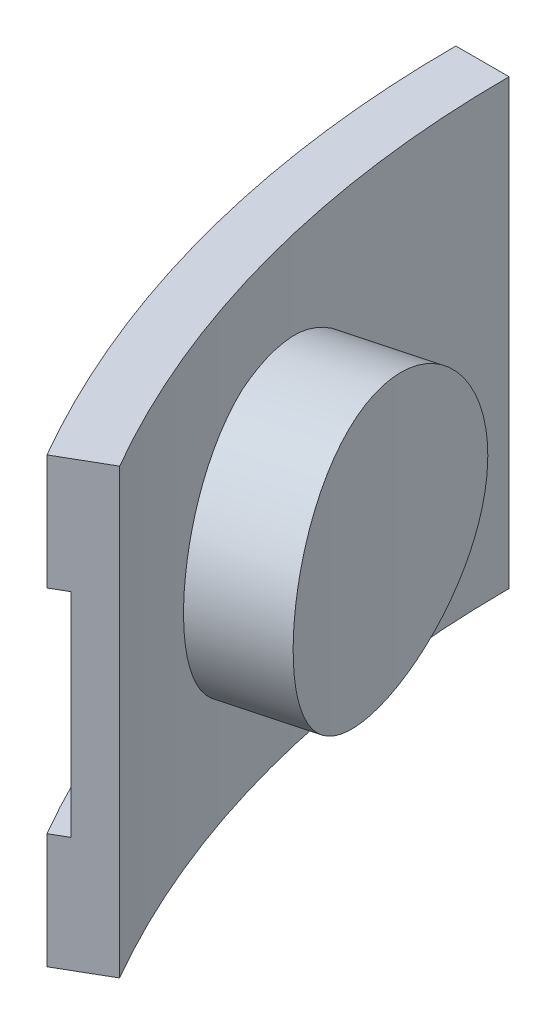
SolidWorks part; units mm, degrees
ref_plane "Front Plane" through (0, 0, 0) normal (0, 0, 1) x (1, 0, 0)
ref_plane "Top Plane" through (0, 0, 0) normal (0, 1, 0) x (1, 0, 0)
ref_plane "Right Plane" through (0, 0, 0) normal (1, 0, 0) x (0, 0, -1)
sketch "Sketch1" plane through (0, 0, 0) normal (0, 0, 1) x (1, 0, 0)
  line L0 (-80.01, 0) -> (-80.01, 8.255)
  line L1 (-80.01, 8.255) -> (-78.74, 8.255)
  line L2 (-78.74, 8.255) -> (-78.74, 23.495)
  line L3 (-78.74, 23.495) -> (-80.01, 23.495)
  line L4 (-80.01, 23.495) -> (-80.01, 31.75)
  line L5 (-80.01, 31.75) -> (-76.2, 31.75)
  line L6 (-76.2, 31.75) -> (-76.2, 0)
  line L7 (-76.2, 0) -> (-80.01, 0)
  line L8 (0, 0) -> (0, 20.32) construction
  dimension "1.25" = 31.75
  dimension "D2" = 76.2
  dimension "D3" = 15.24
  dimension "D4" = 3.81
  dimension "D5" = 2.54
revolve "Revolve1" add sketch "Sketch1" angle 30 about L8
ref_plane "Plane1" through (-71.0956, 0, 19.05) normal (-0.9659, 0, 0.2588) x (0.2588, 0, 0.9659)
sketch "Sketch2" plane through (-71.0956, 0, 19.05) normal (-0.9659, 0, 0.2588) x (0.2588, 0, 0.9659)
  line L0 (0, 0) -> (0, 15.875) construction
  circle A0 centre (0, 15.875) radius 9.8577
  dimension "D2" = 19.7155
  dimension "D1" = 15.875
extrude "Boss-Extrude1" add sketch "Sketch2" along normal blind 2.54
sketch "Sketch3" plane through (-71.0956, 0, 19.05) normal (0.9659, 0, -0.2588) x (-0.2588, 0, -0.9659)
  circle A0 centre (0, 15.875) radius 9.8577
  circle A1 centre (0, 15.875) radius 9.8577 construction
extrude "Boss-Extrude2" add sketch "Sketch3" along normal blind 12.7
sketch "Sketch4" plane through (0, 0, 0) normal (0, 0, 1) x (1, 0, 0)
  line L1 (0, 0) -> (-69.85, 0)
  line L2 (0, 0) -> (0, 31.75)
  line L3 (0, 31.75) -> (-69.85, 31.75)
  line L4 (-69.85, 0) -> (-69.85, 31.75)
  dimension "D1" = 69.85
  dimension "D2" = 31.75
revolve "Cut-Revolve1" cut sketch "Sketch4" angle 30 about L2
